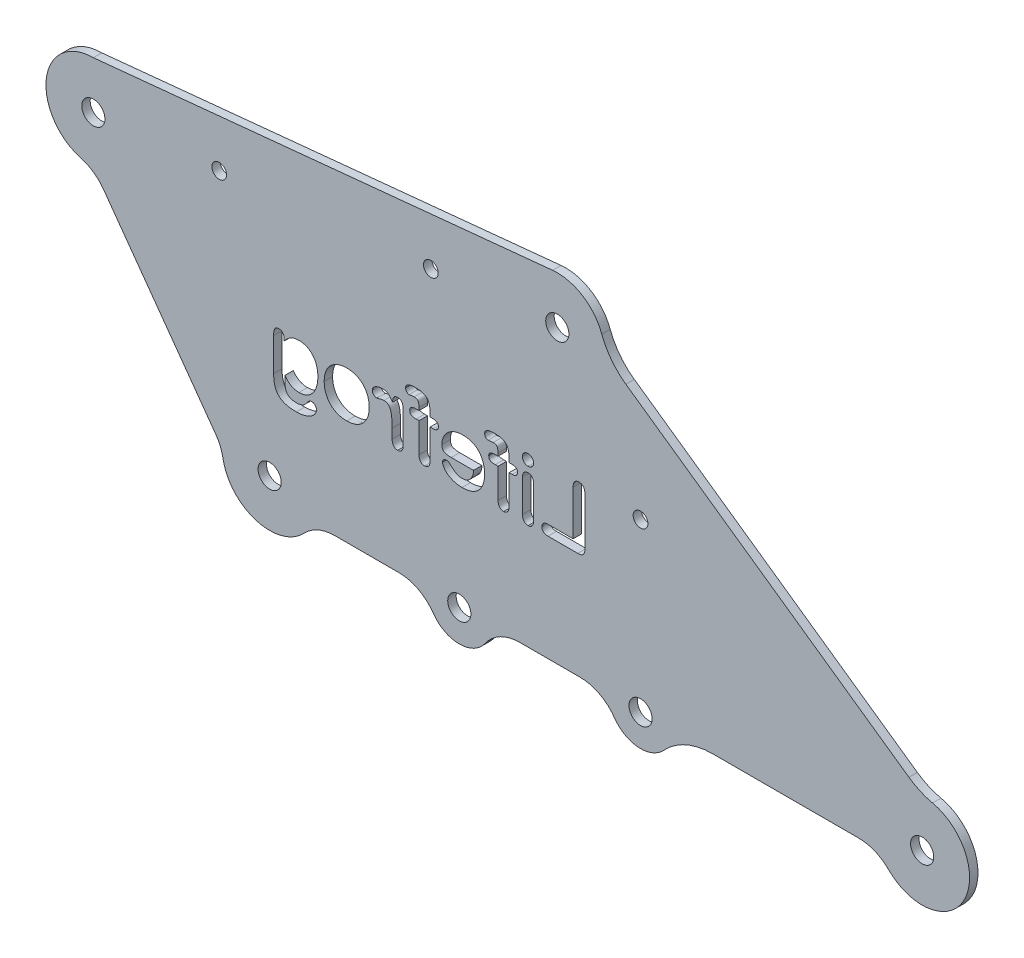
SolidWorks part; units mm, degrees
ref_plane "Front Plane" through (0, 0, 0) normal (0, 0, 1) x (1, 0, 0)
ref_plane "Top Plane" through (0, 0, 0) normal (0, 1, 0) x (1, 0, 0)
ref_plane "Right Plane" through (0, 0, 0) normal (1, 0, 0) x (0, 0, -1)
sketch "Sketch2" plane through (0, 0, 0) normal (0, 0, 1) x (1, 0, 0)
  line L0 (-96.303, -40.0195) -> (103.697, -40.0195) construction
  line L1 (56.1417, 22.4699) -> (-27.5885, 22.4699) construction
  line L2 (56.1417, 22.4699) -> (56.1417, -53.9544) construction
  line L3 (56.1417, -53.9544) -> (-159.2025, -53.9544) construction
  line L4 (-159.2025, 22.4699) -> (-159.2025, -53.9544) construction
  line L5 (-96.303, -40.0195) -> (-53.2713, -40.0195) construction
  line L6 (-100.4268, -47.0897) -> (-100.4268, -59.5897) construction
  line L7 (-100.4268, -59.5897) -> (73.7025, -59.5897) construction
  line L8 (-100.4268, -59.5897) -> (-302.9325, -59.5897) construction
  line L9 (-62.0853, -59.5897) -> (-73.2496, -62.9155) construction
  line L10 (-19.0853, -47.0897) -> (-16.3353, -47.0897) construction
  line L11 (47.7386, -47.0897) -> (47.7386, -41.2921) construction
  line L12 (-62.0853, -47.0897) -> (-107.0853, -47.0897) construction
  line L13 (-107.0853, -47.0897) -> (-107.0853, -42.5195) construction
  line L14 (-62.0853, -47.0897) -> (-59.3353, -47.0897) construction
  line L15 (-167.9726, 11.2199) -> (-124.5853, -42.5195) construction
  line L16 (-124.5853, -42.5195) -> (-167.9726, -37.8951) construction
  line L17 (-167.9726, -37.8951) -> (-167.9726, 11.2199) construction
  line L18 (-167.9726, -37.8951) -> (-167.9726, -59.5897) construction
  line L19 (-146.4823, -3.4151) -> (-119.9002, -40.3454)
  line L21 (-148.9187, 22.4699) -> (-39.9417, 33.2746)
  line L24 (-22.5647, 18.5545) -> (44.5996, -28.6343)
  line L25 (11.3122, -40.0195) -> (103.697, -40.0195) construction
  line L26 (-41.384, 22.4699) -> (-159.2025, 22.4699) construction
  line L27 (-47.7239, -47.0897) -> (-33.4467, -47.0897)
  line L28 (-1.9905, -47.0897) -> (32.6866, -47.0897)
  line L29 (-76.4467, -47.0897) -> (-91.6169, -47.0897)
  line L30 (-54.5853, -47.0897) -> (-19.0853, -47.0897) construction
  line L31 (-11.5853, -47.0897) -> (47.7386, -47.0897) construction
  line L32 (-148.9187, 11.2199) -> (-38.8318, 22.0795) construction
  arc A0 (-26.3612, 21.2219) -> (-51.3257, 22.4699) centre (-38.8318, 22.0795) ccw construction
  circle A1 centre (-38.8318, 22.0795) radius 2.75 construction
  arc A2 (-74.5853, -47.0897) -> (-51.639, -53.9544) centre (-62.0853, -47.0897) ccw construction
  circle A3 centre (-62.0853, -47.0897) radius 2.75 construction
  circle A4 centre (47.7386, -42.0897) radius 2.75
  circle A5 centre (-19.0853, -47.0897) radius 2.75 construction
  circle A6 centre (47.7386, -42.0897) radius 17.5 construction
  circle A7 centre (47.7386, -42.0897) radius 2.75 construction
  circle A8 centre (-107.0853, -42.5195) radius 17.5 construction
  circle A9 centre (-107.0853, -42.5195) radius 2.75 construction
  circle A10 centre (-148.9187, 11.2199) radius 19.0539 construction
  circle A11 centre (-148.9187, 11.2199) radius 2.75 construction
  arc A12 (-148.9187, 22.4699) -> (-151.9256, 0.3791) centre (-148.9187, 11.2199) ccw
  arc A13 (-118.1664, -44.4613) -> (-98.8961, -50.2332) centre (-107.0853, -42.5195) ccw
  arc A14 (-28.2784, 25.9769) -> (-39.9417, 33.2746) centre (-38.8318, 22.0795) ccw
  arc A15 (-68.2402, -51.3754) -> (-55.9304, -51.3754) centre (-62.0853, -47.0897) ccw
  arc A16 (-25.2402, -51.3754) -> (-13.5666, -52.1685) centre (-19.0853, -47.0897) ccw
  arc A17 (39.7699, -50.0309) -> (50.2007, -31.1125) centre (47.7386, -42.0897) ccw
  arc A18 (-7.7098, -42.5525) -> (-9.0853, -40.0195) centre (-19.0853, -47.0897) ccw construction
  arc A19 (-31.8119, -47.0897) -> (-8.3689, -53.9544) centre (-19.0853, -47.0897) ccw construction
  circle A20 centre (-19.0853, -47.0897) radius 2.75
  circle A21 centre (-62.0853, -47.0897) radius 2.75
  circle A22 centre (-107.0853, -42.5195) radius 2.75
  circle A23 centre (-148.9187, 11.2199) radius 2.75
  circle A24 centre (-38.8318, 22.0795) radius 2.75
  arc A25 (32.6866, -47.0897) -> (39.7699, -50.0309) centre (32.6866, -57.0897) cw
  arc A26 (-146.4823, -3.4151) -> (-151.9256, 0.3791) centre (-154.5984, -9.257) ccw
  arc A27 (-119.9002, -40.3454) -> (-118.1664, -44.4613) centre (-128.0164, -46.1873) cw
  arc A28 (-91.6169, -47.0897) -> (-98.8961, -50.2332) centre (-91.6169, -57.0897) ccw
  arc A29 (-76.4467, -47.0897) -> (-68.2402, -51.3754) centre (-76.4467, -57.0897) cw
  arc A30 (-33.4467, -47.0897) -> (-25.2402, -51.3754) centre (-33.4467, -57.0897) cw
  arc A31 (-47.7239, -47.0897) -> (-55.9304, -51.3754) centre (-47.7239, -57.0897) ccw
  arc A33 (-22.5647, 18.5545) -> (-28.2784, 25.9769) centre (-13.5206, 31.4271) cw
  arc A34 (44.5996, -28.6343) -> (50.2007, -31.1125) centre (53.6437, -15.7617) ccw
  arc A35 (-1.9905, -47.0897) -> (-13.5666, -52.1685) centre (-1.9905, -62.8218) ccw
  point P67 (37.6608, -47.0897)
  point P70 (-148.9187, -0.0301)
  point P73 (-118.3353, -42.5195)
  point P76 (-96.8054, -47.0897)
  point P79 (-69.5853, -47.0897)
  point P82 (-26.5853, -47.0897)
  point P91 (-27.5818, 22.0795)
  point P94 (47.7386, -30.8397)
  dimension "D1" = 25
  dimension "D2" = 5.5
  dimension "D5" = 35
  dimension "D6" = 5.5
  dimension "D10" = 22.5
  dimension "D11" = 22.5
  dimension "D12" = 22.5
  dimension "D13" = 5.5
  dimension "D14" = 5.5
  dimension "D15" = 15
  dimension "D16" = 15
  dimension "D17" = 22.5
  dimension "D18" = 10
  dimension "D19" = 5.5
  dimension "D20" = 5.5
  dimension "D3" = 20
  dimension "D4" = 0
  dimension "D7" = 45
  dimension "D8" = 43
  dimension "D9" = 45
extrude "Boss-Extrude1" add sketch "Sketch2" along normal blind 2
sketch "Sketch5" plane through (0, 0, 2) normal (0, 0, 1) x (1, 0, 0)
  line L1 (-106.4284, -21.9146) -> (-30.7738, -21.9146) construction
  line L2 (-106.4284, -21.9146) -> (-106.4284, -6.1743) construction
  line L3 (-106.4284, -6.1743) -> (-30.7738, -6.1743) construction
  line L4 (-30.7738, -21.9146) -> (-30.7738, -6.1743) construction
sketch "Sketch7" plane through (0, 0, 2) normal (0, 0, 1) x (1, 0, 0)
  line L0 (-148.9187, 11.2199) -> (-38.8318, 22.0795) construction
  line L1 (-148.9187, 11.2199) -> (-107.0853, -42.5195) construction
  line L2 (-107.0853, -42.5195) -> (25.9147, -42.5195) construction
  line L3 (25.9147, -42.5195) -> (-38.8318, 22.0795) construction
  line L5 (-107.0853, -2.5195) -> (-35.0853, -2.5195) construction
  line L6 (25.9147, -42.5195) -> (25.9147, -7.5195) construction
  line L7 (25.9147, -7.5195) -> (-64.0853, -7.5195) construction
  circle A0 centre (-119.0636, 14.1649) radius 1.75
  circle A1 centre (-68.8318, 19.1201) radius 1.75
  circle A5 centre (-19.0853, -7.5195) radius 1.75
  dimension "D1" = 3.5
  dimension "D2" = 3.5
  dimension "D4" = 30
  dimension "D5" = 3.5
  dimension "D6" = 40
  dimension "D3" = 30
  dimension "D7" = 35
  dimension "D9" = 45
extrude "Cut-Extrude4" cut sketch "Sketch7" against normal through all
sketch "Sketch8" plane through (0, 0, 0) normal (0, 0, -1) x (-1, 0, 0)
  text T0 "Lifefrog" font "Arial Rounded MT Bold" height 15
extrude "Cut-Extrude5" cut sketch "Sketch8" against normal through all
sketch "Sketch9" plane through (0, 0, 0) normal (0, 0, -1) x (-1, 0, 0)
  line L0 (59.4615, -14.7017) -> (62.4003, -14.7017) construction
  line L1 (59.4615, -12.7672) -> (62.4003, -12.7672)
  line L2 (59.4615, -16.6363) -> (62.4003, -16.6363)
  arc A0 (59.4615, -12.7672) -> (59.4615, -16.6363) centre (59.4615, -14.7017) ccw
  arc A1 (62.4003, -16.6363) -> (62.4003, -12.7672) centre (62.4003, -14.7017) ccw
  circle A2 centre (88.4097, -16.6363) radius 4.4245
  circle A3 centre (101.377, -16.6363) radius 3.8005
  point P2 (60.9309, -14.7017)
extrude "Cut-Extrude6" cut sketch "Sketch9" against normal blind 10
